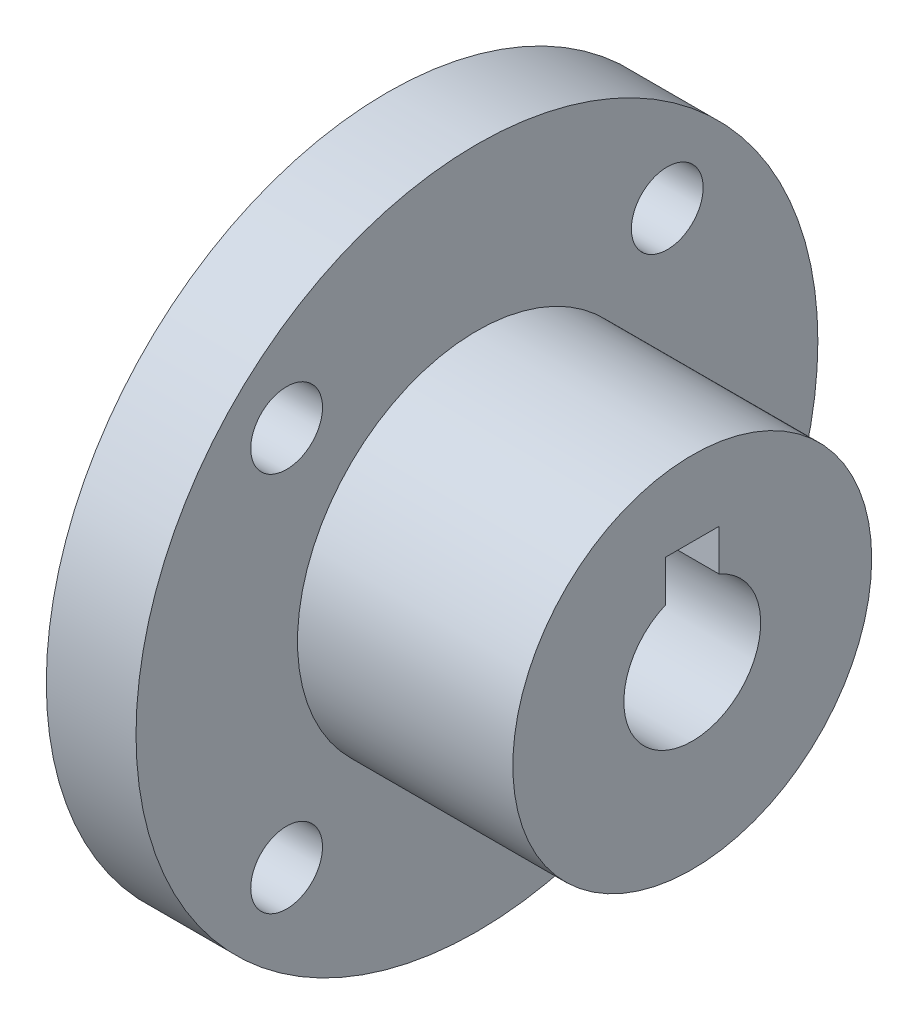
SolidWorks part; units mm, degrees
ref_plane "Piano frontale" through (0, 0, 0) normal (0, 0, 1) x (1, 0, 0)
ref_plane "Piano superiore" through (0, 0, 0) normal (0, 1, 0) x (1, 0, 0)
ref_plane "Piano destro" through (0, 0, 0) normal (1, 0, 0) x (0, 0, -1)
sketch "Sketch1" plane through (0, 0, 0) normal (1, 0, 0) x (0, 0, -1)
  circle A0 centre (0, 0) radius 10
  dimension "D1" = 20
extrude "SmallRing" add sketch "Sketch1" along normal blind 12
sketch "Sketch4" plane through (0, 0, 0) normal (-1, 0, 0) x (0, 0, 1)
  line L0 (-10.6066, 10.6066) -> (10.6066, -10.6066) construction
  line L5 (10.6066, -10.6066) -> (10.6066, 10.6066) construction
  line L6 (10.6066, 10.6066) -> (-10.6066, -10.6066) construction
  line L7 (-10.6066, -10.6066) -> (-10.6066, 10.6066) construction
  line L8 (-10.6066, 10.6066) -> (10.6066, 10.6066) construction
  line L9 (10.6066, -10.6066) -> (-10.6066, -10.6066) construction
  line L10 (-10.6066, 0) -> (10.6066, 0) construction
  circle A0 centre (0, 0) radius 19
  circle A1 centre (0, 0) radius 15 construction
  circle A4 centre (-10.6066, 10.6066) radius 2
  circle A5 centre (10.6066, 10.6066) radius 2
  circle A6 centre (10.6066, -10.6066) radius 2
  circle A7 centre (-10.6066, -10.6066) radius 2
  point P8 (0, 0)
  point P12 (0, 0)
  dimension "D1" = 38
  dimension "D2" = 4
  dimension "D5" = 30
  dimension "D3" = 45
  dimension "D4" = 45
extrude "BigRing" add sketch "Sketch4" along normal blind 5
sketch "Sketch34" plane through (12, 0, 0) normal (1, 0, 0) x (0, 0, -1)
  line L0 (0, 10) -> (0, 0) construction
  circle A0 centre (0, 0) radius 10 construction
sketch "Sketch42" plane through (12, 0, 0) normal (1, 0, 0) x (0, 0, -1)
  circle A0 centre (0, 0) radius 3.8125
  dimension "D1" = 7.625
extrude "Shaft Hole" cut sketch "Sketch42" against normal blind 17
sketch "Sketch43" plane through (12, 0, 0) normal (1, 0, 0) x (0, 0, -1)
  line L0 (-1.5, 5.8125) -> (1.5, 1.8125) construction
  line L5 (-1.5, 5.8125) -> (1.5, 5.8125)
  line L6 (0, 0) -> (0, 3.8125) construction
  line L7 (-1.5, 5.8125) -> (-1.5, 1.8125)
  line L8 (-1.5, 1.8125) -> (1.5, 1.8125)
  line L9 (1.5, 5.8125) -> (1.5, 1.8125)
  line L10 (1.5, 5.8125) -> (-1.5, 1.8125) construction
  line L11 (0, 10) -> (0, 0) construction
  circle A0 centre (0, 0) radius 3.8125 construction
  circle A2 centre (0, 0) radius 3.8125 construction
  point P9 (0, 3.8125)
  point P15 (0, 3.8125)
  dimension "D1" = 4
  dimension "D2" = 3
extrude "KeyWay" cut sketch "Sketch43" against normal blind 17
